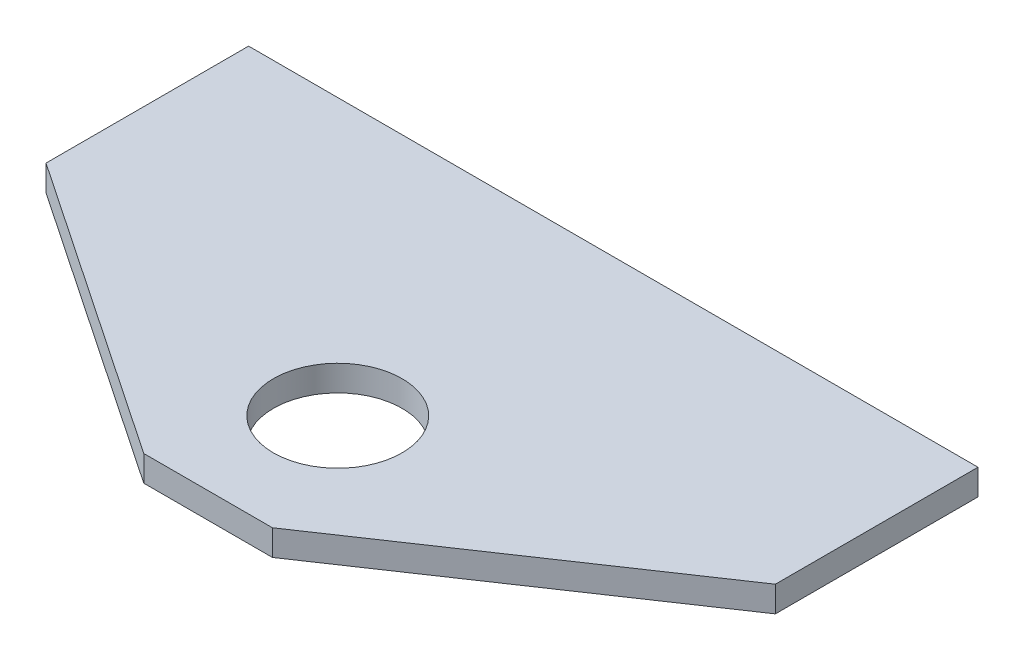
SolidWorks part; units mm, degrees
material "Copper"
ref_plane "Front Plane" through (0, 0, 0) normal (0, 0, 1) x (1, 0, 0)
ref_plane "Top Plane" through (0, 0, 0) normal (0, 1, 0) x (1, 0, 0)
ref_plane "Right Plane" through (0, 0, 0) normal (1, 0, 0) x (0, 0, -1)
sketch "Sketch1" plane through (0, 0, 0) normal (0, 1, 0) x (1, 0, 0)
  line L1 (-22.5, 7.5) -> (22.5, 7.5)
  line L2 (-22.5, 7.5) -> (-22.5, -7.5)
  line L3 (-22.5, -7.5) -> (22.5, -7.5)
  line L4 (22.5, 7.5) -> (22.5, -7.5)
  line L5 (-22.5, 7.5) -> (22.5, -7.5) construction
  line L6 (-22.5, -7.5) -> (22.5, 7.5) construction
  point P0 (0, 0)
  dimension "D1" = 15
  dimension "D2" = 45
sketch "Sketch2" plane through (0, 0, 0) normal (0, 1, 0) x (1, 0, 0)
  line L0 (0, -17) -> (0, 0) construction
  line L1 (-22.5, 0) -> (22.5, 0)
  line L2 (-22.5, 0) -> (-22.5, -25)
  line L3 (-22.5, -25) -> (22.5, -25) construction
  line L4 (22.5, 0) -> (22.5, -25)
  line L5 (22.5, -12.5) -> (3.9688, -25)
  line L6 (-22.5, -12.5) -> (-3.9688, -25)
  line L7 (-3.9688, -25) -> (3.9688, -25)
  circle A0 centre (0, -17) radius 3.9688
  point P0 (0, 0)
  point P13 (0, -25)
  dimension "D3" = 7.9375
  dimension "D1" = 25
  dimension "D2" = 45
  dimension "D4" = 8
  dimension "D5" = 7.9375
extrude "Connector" add sketch "Sketch2" along normal blind 1.5875 contours L6 L7 L5 L4 L1 L2 A0
